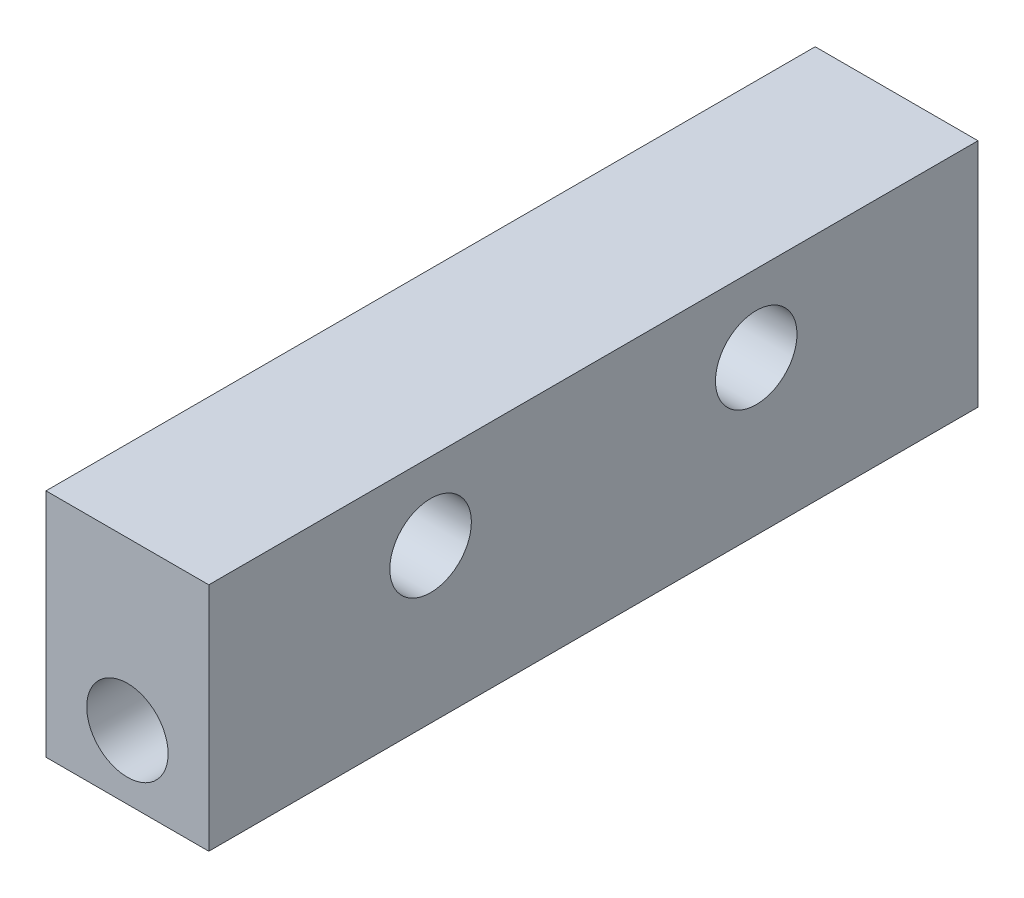
SolidWorks part; units mm, degrees
ref_plane "Front Plane" through (0, 0, 0) normal (0, 0, 1) x (1, 0, 0)
ref_plane "Top Plane" through (0, 0, 0) normal (0, 1, 0) x (1, 0, 0)
ref_plane "Right Plane" through (0, 0, 0) normal (1, 0, 0) x (0, 0, -1)
sketch "Sketch1" plane through (0, 0, 0) normal (0, 0, 1) x (1, 0, 0)
  line L1 (0, 0) -> (6.35, 0)
  line L2 (0, 0) -> (0, -9)
  line L3 (0, -9) -> (6.35, -9)
  line L4 (6.35, 0) -> (6.35, -9)
  circle A0 centre (3.175, -6.5) radius 1.5875
  point P7 (3.175, 0)
  dimension "D3" = 3.175
  dimension "D1" = 9
  dimension "D2" = 6.35
  dimension "D4" = 6.5
extrude "Boss-Extrude1" add sketch "Sketch1" along normal blind 30
sketch "Sketch2" plane through (0, 0, 0) normal (1, 0, 0) x (0, 0, -1)
  line L0 (-30, 0) -> (0, 0) construction
  line L3 (-30, -9) -> (-30, 0) construction
  line L4 (-21.35, -3) -> (-8.65, -3) construction
  circle A0 centre (-21.35, -3) radius 1.59
  circle A1 centre (-8.65, -3) radius 1.59
  dimension "D1" = 3.18
  dimension "D2" = 3
  dimension "D4" = 12.7
  dimension "D3" = 8.65
extrude "Cut-Extrude1" cut sketch "Sketch2" along normal blind 30
equation "\"D3@Sketch2\"=(30-\"D4@Sketch2\")/2"
